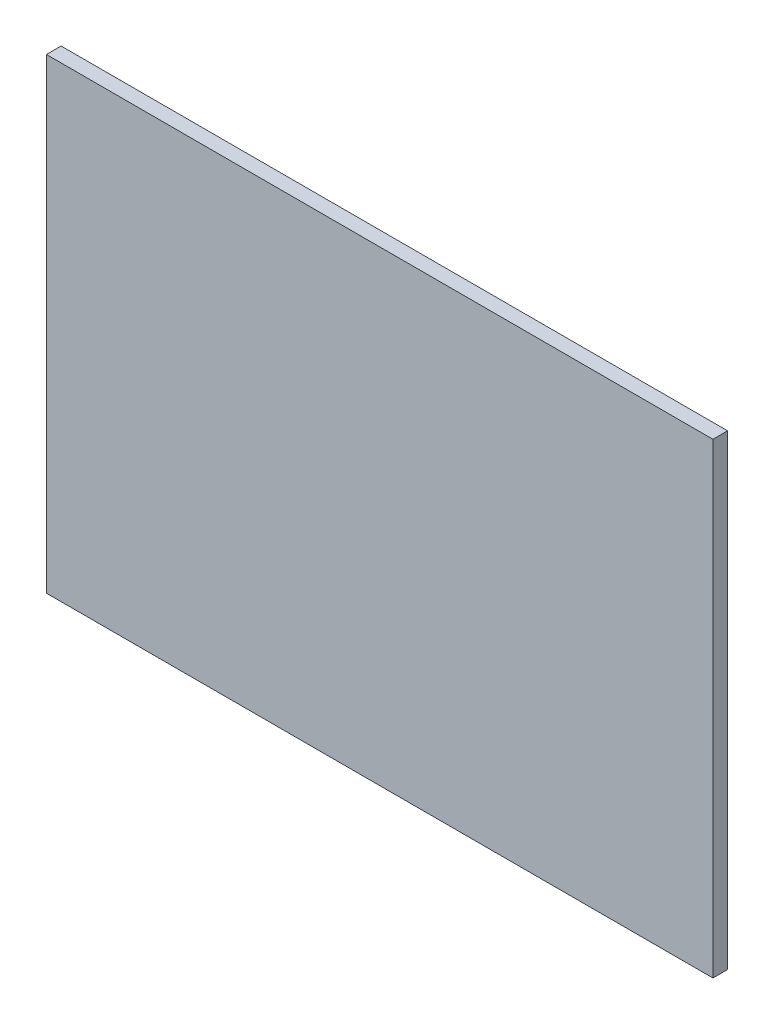
SolidWorks part; units mm, degrees
ref_plane "前视基准面" through (0, 0, 0) normal (0, 0, 1) x (1, 0, 0)
ref_plane "上视基准面" through (0, 0, 0) normal (0, 1, 0) x (1, 0, 0)
ref_plane "右视基准面" through (0, 0, 0) normal (1, 0, 0) x (0, 0, -1)
sketch "草图1" plane through (0, 0, 0) normal (0, 0, 1) x (1, 0, 0)
  line L1 (-25, -17.5) -> (25, -17.5)
  line L2 (-25, -17.5) -> (-25, 17.5)
  line L3 (-25, 17.5) -> (25, 17.5)
  line L4 (25, -17.5) -> (25, 17.5)
  line L5 (-25, -17.5) -> (25, 17.5) construction
  line L6 (-25, 17.5) -> (25, -17.5) construction
  circle A0 centre (0, 0) radius 8.75 construction
  dimension "D1" = 17.5
  dimension "D2" = 35
  dimension "D3" = 50
extrude "凸台-拉伸1" add sketch "草图1" along normal blind 1.1
